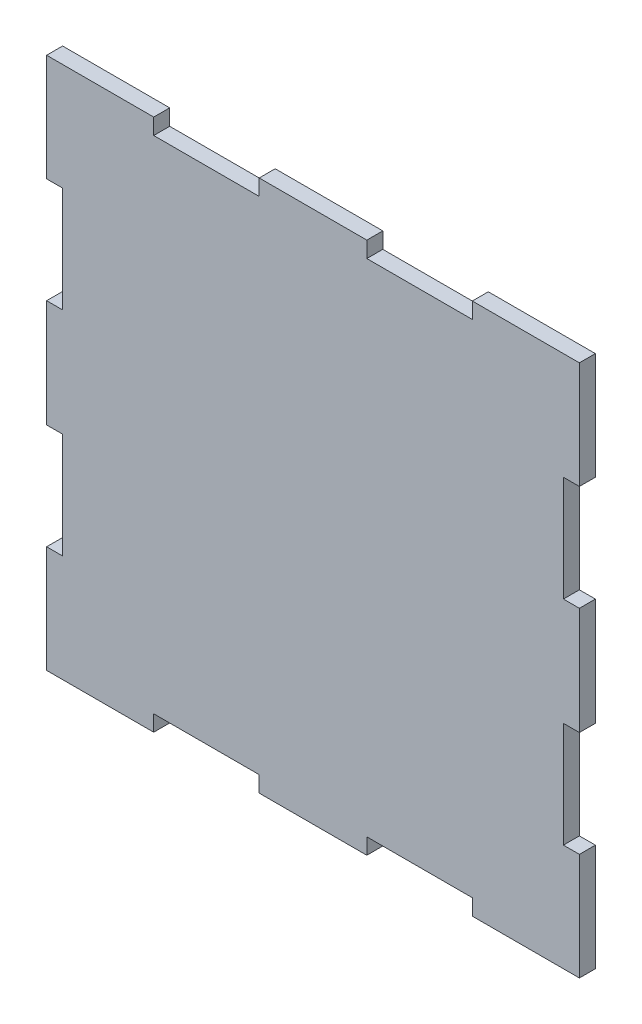
SolidWorks part; units mm, degrees
ref_plane "Front Plane" through (0, 0, 0) normal (0, 0, 1) x (1, 0, 0)
ref_plane "Top Plane" through (0, 0, 0) normal (0, 1, 0) x (1, 0, 0)
ref_plane "Right Plane" through (0, 0, 0) normal (1, 0, 0) x (0, 0, -1)
sketch "Sketch1" plane through (0, 0, 0) normal (0, 0, 1) x (1, 0, 0)
  line L0 (60.1, 100) -> (60.1, 97)
  line L1 (0, 0) -> (100, 0)
  line L2 (0, 0) -> (0, 100)
  line L3 (0, 100) -> (100, 100)
  line L4 (100, 0) -> (100, 100)
  line L5 (20.1, 100) -> (39.9, 100)
  line L6 (20.1, 100) -> (20.1, 97)
  line L7 (20.1, 97) -> (39.9, 97)
  line L8 (39.9, 100) -> (39.9, 97)
  line L9 (60.1, 100) -> (79.9, 100)
  line L10 (79.9, 100) -> (79.9, 97)
  line L11 (60.1, 97) -> (79.9, 97)
  line L12 (0, 39.9) -> (0, 20.1)
  line L13 (0, 79.9) -> (3, 79.9)
  line L14 (0, 79.9) -> (0, 60.1)
  line L15 (0, 60.1) -> (3, 60.1)
  line L16 (3, 79.9) -> (3, 60.1)
  line L17 (0, 39.9) -> (3, 39.9)
  line L18 (3, 39.9) -> (3, 20.1)
  line L19 (0, 20.1) -> (3, 20.1)
  line L20 (100, 50) -> (0, 50) construction
  line L21 (50, -900) -> (50, 49100) construction
  line L22 (20.1, 3) -> (39.9, 3)
  line L23 (39.9, 0) -> (39.9, 3)
  line L24 (20.1, 0) -> (39.9, 0)
  line L25 (20.1, 0) -> (20.1, 3)
  line L26 (60.1, 0) -> (79.9, 0)
  line L27 (79.9, 0) -> (79.9, 3)
  line L28 (60.1, 3) -> (79.9, 3)
  line L29 (60.1, 0) -> (60.1, 3)
  line L30 (100, 39.9) -> (97, 39.9)
  line L31 (97, 39.9) -> (97, 20.1)
  line L32 (100, 20.1) -> (97, 20.1)
  line L33 (100, 39.9) -> (100, 20.1)
  line L34 (100, 60.1) -> (97, 60.1)
  line L35 (97, 79.9) -> (97, 60.1)
  line L36 (100, 79.9) -> (97, 79.9)
  line L37 (100, 79.9) -> (100, 60.1)
  point P26 (50, 100)
  dimension "D1" = 100
  dimension "D2" = 100
  dimension "D3" = 3
  dimension "D4" = 19.8
  dimension "D5" = 20.1
  dimension "D7" = 20.1
  dimension "D8" = 3
  dimension "D9" = 20.1
  dimension "D10" = 19.8
  dimension "D12" = 20.2
  dimension "D6" = 2
  dimension "D11" = 2
extrude "Boss-Extrude1" add sketch "Sketch1" along normal blind 3 contours L36 L4 L3 L10 L11 L0 L8 L7 L6 L2 L13 L16 L15 L17 L18 L19 L1 L25 L22 L23 L29 L28 L27 L32 L31 L30 L34 L35
